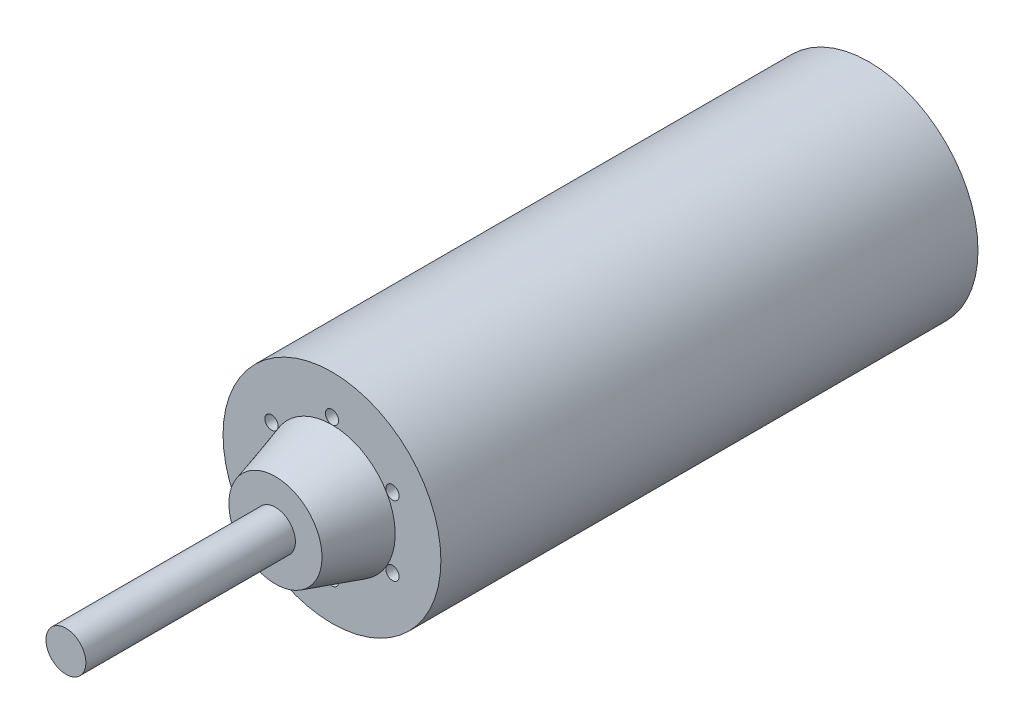
SolidWorks part; units mm, degrees
ref_plane "Front Plane" through (0, 0, 0) normal (0, 0, 1) x (1, 0, 0)
ref_plane "Top Plane" through (0, 0, 0) normal (0, 1, 0) x (1, 0, 0)
ref_plane "Right Plane" through (0, 0, 0) normal (1, 0, 0) x (0, 0, -1)
sketch "Sketch1" plane through (0, 0, 0) normal (0, 0, 1) x (1, 0, 0)
  circle A0 centre (0, 0) radius 32.75
  dimension "D1" = 65.5
extrude "Boss-Extrude1" add sketch "Sketch1" against normal mid plane 161.5
sketch "Sketch10" plane through (0, 0, 0) normal (1, 0, 0) x (0, 0, -1)
  line L0 (-97.75, 0) -> (-97.75, 14)
  line L1 (-80.75, 19) -> (-97.75, 14)
  line L2 (-1000, 0) -> (49000, 0) construction
  line L3 (-97.75, 0) -> (-80.75, 0)
  line L4 (-80.75, 0) -> (-80.75, 19)
  line L6 (-80.75, 32.75) -> (-80.75, -32.75) construction
  point P3 (-97.75, 0)
  dimension "D1" = 14
  dimension "D2" = 17
  dimension "D3" = 19
revolve "Revolve1" add sketch "Sketch10" angle 360 about L2
sketch "Sketch12" plane through (0, 0, 97.75) normal (0, 0, 1) x (1, 0, 0)
  circle A0 centre (0, 0) radius 6
  dimension "D1" = 12
extrude "Boss-Extrude5" add sketch "Sketch12" along normal blind 63
sketch "Sketch13" plane through (0, 0, 80.75) normal (0, 0, 1) x (1, 0, 0)
  line L0 (0, -1000) -> (0, 49000) construction
  circle A0 centre (0, 21) radius 2
  point P4 (0, 21)
  dimension "D2" = 4
  dimension "D1" = 21
extrude "Cut-Extrude1" cut sketch "Sketch13" against normal blind 10
pattern_circular "CirPattern1" count 6 over 360 about axis through (0, 0, 0) along (0, 0, 1) of "Cut-Extrude1"
sketch "Sketch14" plane through (0, 0, -80.75) normal (0, 0, -1) x (-1, 0, 0)
  line L0 (-707.1068, -707.1068) -> (34648.2323, 34648.2323) construction
  circle A0 centre (14.8492, 14.8492) radius 2.5
  point P4 (0, 0)
  dimension "D2" = 5
  dimension "D1" = 21
extrude "Cut-Extrude2" cut sketch "Sketch14" against normal blind 10
pattern_circular "CirPattern2" count 4 over 360 about axis through (0, 0, 0) along (0, 0, 1) of "Cut-Extrude2"
